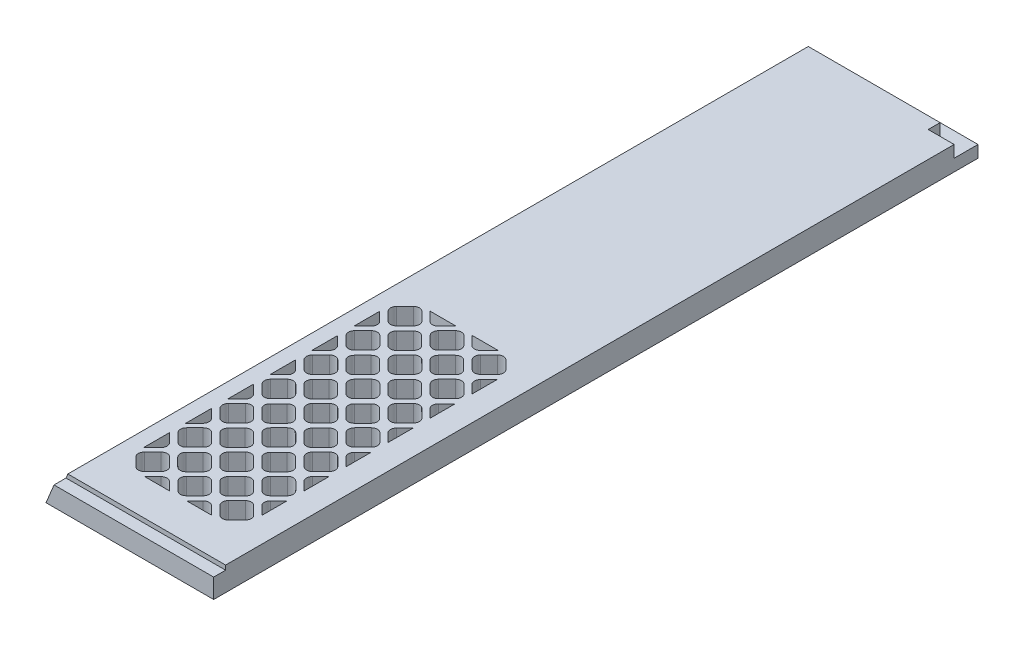
SolidWorks part; units mm, degrees
ref_plane "Front Plane" through (0, 0, 0) normal (0, 0, 1) x (1, 0, 0)
ref_plane "Top Plane" through (0, 0, 0) normal (0, 1, 0) x (1, 0, 0)
ref_plane "Right Plane" through (0, 0, 0) normal (1, 0, 0) x (0, 0, -1)
sketch "Sketch1" plane through (0, 0, 0) normal (0, 0, 1) x (1, 0, 0)
  line L0 (0, 0) -> (5.2605, 12.7)
  line L1 (5.2605, 12.7) -> (89.154, 12.7)
  line L2 (89.154, 12.7) -> (89.154, 0)
  line L3 (89.154, 0) -> (0, 0)
  dimension "D1" = 12.7
  dimension "D2" = 89.154
  dimension "D3" = 67.5
extrude "Boss-Extrude1" add sketch "Sketch1" along normal blind 406.4
sketch "Sketch2" plane through (0, 12.7, 0) normal (0, -1, 0) x (1, 0, 0)
  line L5 (89.154, 406.4) -> (89.154, 0) construction
  line L6 (0, 406.4) -> (89.154, 406.4)
  line L7 (0, 406.4) -> (0, 400.05)
  line L8 (0, 400.05) -> (89.154, 400.05)
  line L9 (89.154, 406.4) -> (89.154, 400.05)
  dimension "D2" = 6.35
extrude "Cut-Extrude1" cut sketch "Sketch2" along normal blind 2.3622
sketch "Sketch3" plane through (0, 0, 0) normal (0, -1, 0) x (1, 0, 0)
  line L90 (0, 203.2) -> (89.154, 203.2) construction
  line L91 (0, 406.4) -> (0, 0) construction
  line L221 (89.154, 406.4) -> (89.154, 0) construction
  line L222 (13.3842, 233.4919) -> (17.8743, 229.0018)
  line L223 (17.8743, 246.8637) -> (13.3842, 242.3736)
  line L235 (13.3842, 255.8439) -> (17.8743, 251.3538)
  line L236 (17.8743, 269.2157) -> (13.3842, 264.7256)
  line L237 (13.3842, 278.1959) -> (17.8743, 273.7058)
  line L238 (17.8743, 291.5677) -> (13.3842, 287.0776)
  line L239 (13.3842, 300.5479) -> (17.8743, 296.0578)
  line L240 (17.8743, 313.9197) -> (13.3842, 309.4296)
  line L241 (13.3842, 322.8999) -> (17.8743, 318.4098)
  line L242 (17.8743, 336.2717) -> (13.3842, 331.7816)
  line L243 (13.3842, 345.2519) -> (17.8743, 340.7618)
  line L244 (17.8743, 358.6237) -> (13.3842, 354.1336)
  line L245 (13.3842, 367.6039) -> (17.8743, 363.1138)
  line L246 (71.4599, 229.0018) -> (75.9093, 233.4512)
  line L247 (49.1079, 229.0018) -> (53.598, 233.4919)
  line L248 (58.0882, 233.4919) -> (62.5783, 229.0018)
  line L249 (26.7559, 229.0018) -> (31.246, 233.4919)
  line L250 (35.7362, 233.4919) -> (40.2263, 229.0018)
  line L251 (71.4599, 251.3538) -> (75.9093, 255.8032)
  line L252 (75.9093, 242.4143) -> (71.4599, 246.8637)
  line L253 (49.1079, 251.3538) -> (53.598, 255.8439)
  line L254 (53.598, 242.3736) -> (49.1079, 246.8637)
  line L255 (62.5783, 246.8637) -> (58.0882, 242.3736)
  line L256 (58.0882, 255.8439) -> (62.5783, 251.3538)
  line L257 (26.7559, 251.3538) -> (31.246, 255.8439)
  line L258 (31.246, 242.3736) -> (26.7559, 246.8637)
  line L259 (40.2263, 246.8637) -> (35.7362, 242.3736)
  line L260 (35.7362, 255.8439) -> (40.2263, 251.3538)
  line L261 (71.4599, 273.7058) -> (75.9093, 278.1552)
  line L262 (75.9093, 264.7663) -> (71.4599, 269.2157)
  line L263 (49.1079, 273.7058) -> (53.598, 278.1959)
  line L264 (53.598, 264.7256) -> (49.1079, 269.2157)
  line L265 (62.5783, 269.2157) -> (58.0882, 264.7256)
  line L266 (58.0882, 278.1959) -> (62.5783, 273.7058)
  line L267 (26.7559, 273.7058) -> (31.246, 278.1959)
  line L268 (31.246, 264.7256) -> (26.7559, 269.2157)
  line L269 (40.2263, 269.2157) -> (35.7362, 264.7256)
  line L270 (35.7362, 278.1959) -> (40.2263, 273.7058)
  line L271 (71.4599, 296.0578) -> (75.9093, 300.5072)
  line L272 (75.9093, 287.1183) -> (71.4599, 291.5677)
  line L273 (49.1079, 296.0578) -> (53.598, 300.5479)
  line L274 (53.598, 287.0776) -> (49.1079, 291.5677)
  line L275 (62.5783, 291.5677) -> (58.0882, 287.0776)
  line L276 (58.0882, 300.5479) -> (62.5783, 296.0578)
  line L277 (26.7559, 296.0578) -> (31.246, 300.5479)
  line L278 (31.246, 287.0776) -> (26.7559, 291.5677)
  line L279 (40.2263, 291.5677) -> (35.7362, 287.0776)
  line L280 (35.7362, 300.5479) -> (40.2263, 296.0578)
  line L281 (71.4599, 318.4098) -> (75.9093, 322.8592)
  line L282 (75.9093, 309.4703) -> (71.4599, 313.9197)
  line L283 (49.1079, 318.4098) -> (53.598, 322.8999)
  line L284 (53.598, 309.4296) -> (49.1079, 313.9197)
  line L285 (62.5783, 313.9197) -> (58.0882, 309.4296)
  line L286 (58.0882, 322.8999) -> (62.5783, 318.4098)
  line L287 (26.7559, 318.4098) -> (31.246, 322.8999)
  line L288 (31.246, 309.4296) -> (26.7559, 313.9197)
  line L289 (40.2263, 313.9197) -> (35.7362, 309.4296)
  line L290 (35.7362, 322.8999) -> (40.2263, 318.4098)
  line L291 (71.4599, 340.7618) -> (75.9093, 345.2112)
  line L292 (75.9093, 331.8223) -> (71.4599, 336.2717)
  line L293 (49.1079, 340.7618) -> (53.598, 345.2519)
  line L294 (53.598, 331.7816) -> (49.1079, 336.2717)
  line L295 (62.5783, 336.2717) -> (58.0882, 331.7816)
  line L296 (58.0882, 345.2519) -> (62.5783, 340.7618)
  line L297 (26.7559, 340.7618) -> (31.246, 345.2519)
  line L298 (31.246, 331.7816) -> (26.7559, 336.2717)
  line L299 (40.2263, 336.2717) -> (35.7362, 331.7816)
  line L300 (35.7362, 345.2519) -> (40.2263, 340.7618)
  line L301 (71.4599, 363.1138) -> (75.9093, 367.5632)
  line L302 (75.9093, 354.1743) -> (71.4599, 358.6237)
  line L303 (49.1079, 363.1138) -> (53.598, 367.6039)
  line L304 (53.598, 354.1336) -> (49.1079, 358.6237)
  line L305 (62.5783, 358.6237) -> (58.0882, 354.1336)
  line L306 (58.0882, 367.6039) -> (62.5783, 363.1138)
  line L307 (26.7559, 363.1138) -> (31.246, 367.6039)
  line L308 (31.246, 354.1336) -> (26.7559, 358.6237)
  line L309 (40.2263, 358.6237) -> (35.7362, 354.1336)
  line L310 (35.7362, 367.6039) -> (40.2263, 363.1138)
  line L311 (75.9093, 376.5263) -> (71.5993, 380.8363)
  line L312 (53.598, 376.4856) -> (49.2473, 380.8363)
  line L313 (62.4389, 380.8363) -> (58.0882, 376.4856)
  line L314 (31.246, 376.4856) -> (26.8953, 380.8363)
  line L315 (40.0869, 380.8363) -> (35.7362, 376.4856)
  line L316 (17.7349, 380.8363) -> (13.3842, 376.4856)
  line L317 (73.6642, 235.4989) -> (69.1741, 231.0088)
  line L318 (69.1741, 244.4792) -> (73.6642, 239.9891)
  line L319 (60.1938, 239.9891) -> (64.6839, 244.4792)
  line L320 (64.6839, 231.0088) -> (60.1938, 235.4989)
  line L321 (51.3122, 235.4989) -> (46.8221, 231.0088)
  line L322 (46.8221, 244.4792) -> (51.3122, 239.9891)
  line L323 (37.8418, 239.9891) -> (42.3319, 244.4792)
  line L324 (42.3319, 231.0088) -> (37.8418, 235.4989)
  line L325 (28.9602, 235.4989) -> (24.4701, 231.0088)
  line L326 (24.4701, 244.4792) -> (28.9602, 239.9891)
  line L327 (15.4898, 239.9891) -> (19.9799, 244.4792)
  line L328 (19.9799, 231.0088) -> (15.4898, 235.4989)
  line L329 (73.6642, 257.8509) -> (69.1741, 253.3608)
  line L330 (69.1741, 266.8312) -> (73.6642, 262.3411)
  line L331 (60.1938, 262.3411) -> (64.6839, 266.8312)
  line L332 (64.6839, 253.3608) -> (60.1938, 257.8509)
  line L333 (51.3122, 257.8509) -> (46.8221, 253.3608)
  line L334 (46.8221, 266.8312) -> (51.3122, 262.3411)
  line L335 (37.8418, 262.3411) -> (42.3319, 266.8312)
  line L336 (42.3319, 253.3608) -> (37.8418, 257.8509)
  line L337 (28.9602, 257.8509) -> (24.4701, 253.3608)
  line L338 (24.4701, 266.8312) -> (28.9602, 262.3411)
  line L339 (15.4898, 262.3411) -> (19.9799, 266.8312)
  line L340 (19.9799, 253.3608) -> (15.4898, 257.8509)
  line L341 (73.6642, 280.2029) -> (69.1741, 275.7128)
  line L342 (69.1741, 289.1832) -> (73.6642, 284.6931)
  line L343 (60.1938, 284.6931) -> (64.6839, 289.1832)
  line L344 (64.6839, 275.7128) -> (60.1938, 280.2029)
  line L345 (51.3122, 280.2029) -> (46.8221, 275.7128)
  line L346 (46.8221, 289.1832) -> (51.3122, 284.6931)
  line L347 (37.8418, 284.6931) -> (42.3319, 289.1832)
  line L348 (42.3319, 275.7128) -> (37.8418, 280.2029)
  line L349 (28.9602, 280.2029) -> (24.4701, 275.7128)
  line L350 (24.4701, 289.1832) -> (28.9602, 284.6931)
  line L351 (15.4898, 284.6931) -> (19.9799, 289.1832)
  line L352 (19.9799, 275.7128) -> (15.4898, 280.2029)
  line L353 (73.6642, 302.5549) -> (69.1741, 298.0648)
  line L354 (69.1741, 311.5352) -> (73.6642, 307.0451)
  line L355 (60.1938, 307.0451) -> (64.6839, 311.5352)
  line L356 (64.6839, 298.0648) -> (60.1938, 302.5549)
  line L357 (51.3122, 302.5549) -> (46.8221, 298.0648)
  line L358 (46.8221, 311.5352) -> (51.3122, 307.0451)
  line L359 (37.8418, 307.0451) -> (42.3319, 311.5352)
  line L360 (42.3319, 298.0648) -> (37.8418, 302.5549)
  line L361 (28.9602, 302.5549) -> (24.4701, 298.0648)
  line L362 (24.4701, 311.5352) -> (28.9602, 307.0451)
  line L363 (15.4898, 307.0451) -> (19.9799, 311.5352)
  line L364 (19.9799, 298.0648) -> (15.4898, 302.5549)
  line L365 (73.6642, 324.9069) -> (69.1741, 320.4168)
  line L366 (69.1741, 333.8872) -> (73.6642, 329.3971)
  line L367 (60.1938, 329.3971) -> (64.6839, 333.8872)
  line L368 (64.6839, 320.4168) -> (60.1938, 324.9069)
  line L369 (51.3122, 324.9069) -> (46.8221, 320.4168)
  line L370 (46.8221, 333.8872) -> (51.3122, 329.3971)
  line L371 (37.8418, 329.3971) -> (42.3319, 333.8872)
  line L372 (42.3319, 320.4168) -> (37.8418, 324.9069)
  line L373 (28.9602, 324.9069) -> (24.4701, 320.4168)
  line L374 (24.4701, 333.8872) -> (28.9602, 329.3971)
  line L375 (15.4898, 329.3971) -> (19.9799, 333.8872)
  line L376 (19.9799, 320.4168) -> (15.4898, 324.9069)
  line L377 (73.6642, 347.2589) -> (69.1741, 342.7688)
  line L378 (69.1741, 356.2392) -> (73.6642, 351.7491)
  line L379 (60.1938, 351.7491) -> (64.6839, 356.2392)
  line L380 (64.6839, 342.7688) -> (60.1938, 347.2589)
  line L381 (51.3122, 347.2589) -> (46.8221, 342.7688)
  line L382 (46.8221, 356.2392) -> (51.3122, 351.7491)
  line L383 (37.8418, 351.7491) -> (42.3319, 356.2392)
  line L384 (42.3319, 342.7688) -> (37.8418, 347.2589)
  line L385 (28.9602, 347.2589) -> (24.4701, 342.7688)
  line L386 (24.4701, 356.2392) -> (28.9602, 351.7491)
  line L387 (15.4898, 351.7491) -> (19.9799, 356.2392)
  line L388 (19.9799, 342.7688) -> (15.4898, 347.2589)
  line L389 (73.6642, 369.6109) -> (69.1741, 365.1208)
  line L390 (69.1741, 378.5912) -> (73.6642, 374.1011)
  line L391 (60.1938, 374.1011) -> (64.6839, 378.5912)
  line L392 (64.6839, 365.1208) -> (60.1938, 369.6109)
  line L393 (51.3122, 369.6109) -> (46.8221, 365.1208)
  line L394 (46.8221, 378.5912) -> (51.3122, 374.1011)
  line L395 (37.8418, 374.1011) -> (42.3319, 378.5912)
  line L396 (42.3319, 365.1208) -> (37.8418, 369.6109)
  line L397 (19.9799, 365.1208) -> (15.4898, 369.6109)
  line L398 (28.9602, 369.6109) -> (24.4701, 365.1208)
  line L399 (24.4701, 378.5912) -> (28.9602, 374.1011)
  line L400 (75.9093, 380.8363) -> (75.9093, 228.7637)
  line L401 (13.2447, 228.7637) -> (75.9093, 228.7637)
  line L402 (13.2447, 380.8363) -> (13.2447, 228.7637)
  line L403 (13.2447, 380.8363) -> (75.9093, 380.8363)
  line L404 (15.4898, 374.1011) -> (19.9799, 378.5912)
  arc A212 (18.0894, 228.7637) -> (17.8743, 229.0018) centre (15.6292, 226.7568) ccw
  arc A224 (13.2447, 233.6232) -> (13.3842, 233.4919) centre (11.1391, 231.2469) cw
  arc A225 (13.3842, 242.3736) -> (13.2447, 242.2423) centre (11.1391, 244.6186) cw
  arc A226 (17.8743, 246.8637) -> (17.8743, 251.3538) centre (15.6292, 249.1088) ccw
  arc A227 (13.2447, 255.9752) -> (13.3842, 255.8439) centre (11.1391, 253.5989) cw
  arc A228 (13.3842, 264.7256) -> (13.2447, 264.5943) centre (11.1391, 266.9706) cw
  arc A229 (17.8743, 269.2157) -> (17.8743, 273.7058) centre (15.6292, 271.4608) ccw
  arc A230 (13.2447, 278.3272) -> (13.3842, 278.1959) centre (11.1391, 275.9509) cw
  arc A231 (13.3842, 287.0776) -> (13.2447, 286.9463) centre (11.1391, 289.3226) cw
  arc A232 (17.8743, 291.5677) -> (17.8743, 296.0578) centre (15.6292, 293.8128) ccw
  arc A233 (13.2447, 300.6792) -> (13.3842, 300.5479) centre (11.1391, 298.3029) cw
  arc A234 (13.3842, 309.4296) -> (13.2447, 309.2983) centre (11.1391, 311.6746) cw
  arc A235 (17.8743, 313.9197) -> (17.8743, 318.4098) centre (15.6292, 316.1648) ccw
  arc A236 (13.2447, 323.0312) -> (13.3842, 322.8999) centre (11.1391, 320.6549) cw
  arc A237 (13.3842, 331.7816) -> (13.2447, 331.6503) centre (11.1391, 334.0266) cw
  arc A238 (17.8743, 336.2717) -> (17.8743, 340.7618) centre (15.6292, 338.5168) ccw
  arc A239 (13.2447, 345.3832) -> (13.3842, 345.2519) centre (11.1391, 343.0069) cw
  arc A240 (13.3842, 354.1336) -> (13.2447, 354.0023) centre (11.1391, 356.3786) cw
  arc A241 (17.8743, 358.6237) -> (17.8743, 363.1138) centre (15.6292, 360.8688) ccw
  arc A242 (13.2447, 367.7352) -> (13.3842, 367.6039) centre (11.1391, 365.3589) cw
  arc A243 (71.2448, 228.7637) -> (71.4599, 229.0018) centre (73.705, 226.7568) cw
  arc A244 (48.8928, 228.7637) -> (49.1079, 229.0018) centre (51.353, 226.7568) cw
  arc A245 (62.7934, 228.7637) -> (62.5783, 229.0018) centre (60.3332, 226.7568) ccw
  arc A246 (53.598, 233.4919) -> (58.0882, 233.4919) centre (55.8431, 231.2469) cw
  arc A247 (26.5408, 228.7637) -> (26.7559, 229.0018) centre (29.001, 226.7568) cw
  arc A248 (40.4414, 228.7637) -> (40.2263, 229.0018) centre (37.9812, 226.7568) ccw
  arc A249 (31.246, 233.4919) -> (35.7362, 233.4919) centre (33.4911, 231.2469) cw
  arc A250 (71.4599, 246.8637) -> (71.4599, 251.3538) centre (73.705, 249.1088) cw
  arc A251 (49.1079, 246.8637) -> (49.1079, 251.3538) centre (51.353, 249.1088) cw
  arc A252 (58.0882, 242.3736) -> (53.598, 242.3736) centre (55.8431, 244.6186) cw
  arc A253 (62.5783, 246.8637) -> (62.5783, 251.3538) centre (60.3332, 249.1088) ccw
  arc A254 (53.598, 255.8439) -> (58.0882, 255.8439) centre (55.8431, 253.5989) cw
  arc A255 (26.7559, 246.8637) -> (26.7559, 251.3538) centre (29.001, 249.1088) cw
  arc A256 (35.7362, 242.3736) -> (31.246, 242.3736) centre (33.4911, 244.6186) cw
  arc A257 (40.2263, 246.8637) -> (40.2263, 251.3538) centre (37.9812, 249.1088) ccw
  arc A258 (31.246, 255.8439) -> (35.7362, 255.8439) centre (33.4911, 253.5989) cw
  arc A259 (71.4599, 269.2157) -> (71.4599, 273.7058) centre (73.705, 271.4608) cw
  arc A260 (49.1079, 269.2157) -> (49.1079, 273.7058) centre (51.353, 271.4608) cw
  arc A261 (58.0882, 264.7256) -> (53.598, 264.7256) centre (55.8431, 266.9706) cw
  arc A262 (62.5783, 269.2157) -> (62.5783, 273.7058) centre (60.3332, 271.4608) ccw
  arc A263 (53.598, 278.1959) -> (58.0882, 278.1959) centre (55.8431, 275.9509) cw
  arc A264 (26.7559, 269.2157) -> (26.7559, 273.7058) centre (29.001, 271.4608) cw
  arc A265 (35.7362, 264.7256) -> (31.246, 264.7256) centre (33.4911, 266.9706) cw
  arc A266 (40.2263, 269.2157) -> (40.2263, 273.7058) centre (37.9812, 271.4608) ccw
  arc A267 (31.246, 278.1959) -> (35.7362, 278.1959) centre (33.4911, 275.9509) cw
  arc A268 (71.4599, 291.5677) -> (71.4599, 296.0578) centre (73.705, 293.8128) cw
  arc A269 (49.1079, 291.5677) -> (49.1079, 296.0578) centre (51.353, 293.8128) cw
  arc A270 (58.0882, 287.0776) -> (53.598, 287.0776) centre (55.8431, 289.3226) cw
  arc A271 (62.5783, 291.5677) -> (62.5783, 296.0578) centre (60.3332, 293.8128) ccw
  arc A272 (53.598, 300.5479) -> (58.0882, 300.5479) centre (55.8431, 298.3029) cw
  arc A273 (26.7559, 291.5677) -> (26.7559, 296.0578) centre (29.001, 293.8128) cw
  arc A274 (35.7362, 287.0776) -> (31.246, 287.0776) centre (33.4911, 289.3226) cw
  arc A275 (40.2263, 291.5677) -> (40.2263, 296.0578) centre (37.9812, 293.8128) ccw
  arc A276 (31.246, 300.5479) -> (35.7362, 300.5479) centre (33.4911, 298.3029) cw
  arc A277 (71.4599, 313.9197) -> (71.4599, 318.4098) centre (73.705, 316.1648) cw
  arc A278 (49.1079, 313.9197) -> (49.1079, 318.4098) centre (51.353, 316.1648) cw
  arc A279 (58.0882, 309.4296) -> (53.598, 309.4296) centre (55.8431, 311.6746) cw
  arc A280 (62.5783, 313.9197) -> (62.5783, 318.4098) centre (60.3332, 316.1648) ccw
  arc A281 (53.598, 322.8999) -> (58.0882, 322.8999) centre (55.8431, 320.6549) cw
  arc A282 (26.7559, 313.9197) -> (26.7559, 318.4098) centre (29.001, 316.1648) cw
  arc A283 (35.7362, 309.4296) -> (31.246, 309.4296) centre (33.4911, 311.6746) cw
  arc A284 (40.2263, 313.9197) -> (40.2263, 318.4098) centre (37.9812, 316.1648) ccw
  arc A285 (31.246, 322.8999) -> (35.7362, 322.8999) centre (33.4911, 320.6549) cw
  arc A286 (71.4599, 336.2717) -> (71.4599, 340.7618) centre (73.705, 338.5168) cw
  arc A287 (49.1079, 336.2717) -> (49.1079, 340.7618) centre (51.353, 338.5168) cw
  arc A288 (58.0882, 331.7816) -> (53.598, 331.7816) centre (55.8431, 334.0266) cw
  arc A289 (62.5783, 336.2717) -> (62.5783, 340.7618) centre (60.3332, 338.5168) ccw
  arc A290 (53.598, 345.2519) -> (58.0882, 345.2519) centre (55.8431, 343.0069) cw
  arc A291 (26.7559, 336.2717) -> (26.7559, 340.7618) centre (29.001, 338.5168) cw
  arc A292 (35.7362, 331.7816) -> (31.246, 331.7816) centre (33.4911, 334.0266) cw
  arc A293 (40.2263, 336.2717) -> (40.2263, 340.7618) centre (37.9812, 338.5168) ccw
  arc A294 (31.246, 345.2519) -> (35.7362, 345.2519) centre (33.4911, 343.0069) cw
  arc A295 (71.4599, 358.6237) -> (71.4599, 363.1138) centre (73.705, 360.8688) cw
  arc A296 (49.1079, 358.6237) -> (49.1079, 363.1138) centre (51.353, 360.8688) cw
  arc A297 (58.0882, 354.1336) -> (53.598, 354.1336) centre (55.8431, 356.3786) cw
  arc A298 (62.5783, 358.6237) -> (62.5783, 363.1138) centre (60.3332, 360.8688) ccw
  arc A299 (53.598, 367.6039) -> (58.0882, 367.6039) centre (55.8431, 365.3589) cw
  arc A300 (26.7559, 358.6237) -> (26.7559, 363.1138) centre (29.001, 360.8688) cw
  arc A301 (35.7362, 354.1336) -> (31.246, 354.1336) centre (33.4911, 356.3786) cw
  arc A302 (40.2263, 358.6237) -> (40.2263, 363.1138) centre (37.9812, 360.8688) ccw
  arc A303 (31.246, 367.6039) -> (35.7362, 367.6039) centre (33.4911, 365.3589) cw
  arc A304 (58.0882, 376.4856) -> (53.598, 376.4856) centre (55.8431, 378.7306) cw
  arc A305 (35.7362, 376.4856) -> (31.246, 376.4856) centre (33.4911, 378.7306) cw
  arc A306 (13.3842, 376.4856) -> (13.2447, 376.3543) centre (11.1391, 378.7306) cw
  arc A307 (69.1741, 231.0088) -> (64.6839, 231.0088) centre (66.929, 233.2539) cw
  arc A308 (73.6642, 239.9891) -> (73.6642, 235.4989) centre (71.4191, 237.744) cw
  arc A309 (64.6839, 244.4792) -> (69.1741, 244.4792) centre (66.929, 242.2341) cw
  arc A310 (60.1938, 239.9891) -> (60.1938, 235.4989) centre (62.4389, 237.744) ccw
  arc A311 (46.8221, 231.0088) -> (42.3319, 231.0088) centre (44.577, 233.2539) cw
  arc A312 (51.3122, 239.9891) -> (51.3122, 235.4989) centre (49.0671, 237.744) cw
  arc A313 (42.3319, 244.4792) -> (46.8221, 244.4792) centre (44.577, 242.2341) cw
  arc A314 (37.8418, 239.9891) -> (37.8418, 235.4989) centre (40.0869, 237.744) ccw
  arc A315 (28.9602, 239.9891) -> (28.9602, 235.4989) centre (26.7151, 237.744) cw
  arc A316 (19.9799, 244.4792) -> (24.4701, 244.4792) centre (22.225, 242.2341) cw
  arc A317 (24.4701, 231.0088) -> (19.9799, 231.0088) centre (22.225, 233.2539) cw
  arc A318 (15.4898, 239.9891) -> (15.4898, 235.4989) centre (17.7349, 237.744) ccw
  arc A319 (69.1741, 253.3608) -> (64.6839, 253.3608) centre (66.929, 255.6059) cw
  arc A320 (73.6642, 262.3411) -> (73.6642, 257.8509) centre (71.4191, 260.096) cw
  arc A321 (64.6839, 266.8312) -> (69.1741, 266.8312) centre (66.929, 264.5861) cw
  arc A322 (60.1938, 262.3411) -> (60.1938, 257.8509) centre (62.4389, 260.096) ccw
  arc A323 (46.8221, 253.3608) -> (42.3319, 253.3608) centre (44.577, 255.6059) cw
  arc A324 (51.3122, 262.3411) -> (51.3122, 257.8509) centre (49.0671, 260.096) cw
  arc A325 (42.3319, 266.8312) -> (46.8221, 266.8312) centre (44.577, 264.5861) cw
  arc A326 (37.8418, 262.3411) -> (37.8418, 257.8509) centre (40.0869, 260.096) ccw
  arc A327 (28.9602, 262.3411) -> (28.9602, 257.8509) centre (26.7151, 260.096) cw
  arc A328 (19.9799, 266.8312) -> (24.4701, 266.8312) centre (22.225, 264.5861) cw
  arc A329 (24.4701, 253.3608) -> (19.9799, 253.3608) centre (22.225, 255.6059) cw
  arc A330 (15.4898, 262.3411) -> (15.4898, 257.8509) centre (17.7349, 260.096) ccw
  arc A331 (69.1741, 275.7128) -> (64.6839, 275.7128) centre (66.929, 277.9579) cw
  arc A332 (73.6642, 284.6931) -> (73.6642, 280.2029) centre (71.4191, 282.448) cw
  arc A333 (64.6839, 289.1832) -> (69.1741, 289.1832) centre (66.929, 286.9381) cw
  arc A334 (60.1938, 284.6931) -> (60.1938, 280.2029) centre (62.4389, 282.448) ccw
  arc A335 (46.8221, 275.7128) -> (42.3319, 275.7128) centre (44.577, 277.9579) cw
  arc A336 (51.3122, 284.6931) -> (51.3122, 280.2029) centre (49.0671, 282.448) cw
  arc A337 (42.3319, 289.1832) -> (46.8221, 289.1832) centre (44.577, 286.9381) cw
  arc A338 (37.8418, 284.6931) -> (37.8418, 280.2029) centre (40.0869, 282.448) ccw
  arc A339 (28.9602, 284.6931) -> (28.9602, 280.2029) centre (26.7151, 282.448) cw
  arc A340 (19.9799, 289.1832) -> (24.4701, 289.1832) centre (22.225, 286.9381) cw
  arc A341 (24.4701, 275.7128) -> (19.9799, 275.7128) centre (22.225, 277.9579) cw
  arc A342 (15.4898, 284.6931) -> (15.4898, 280.2029) centre (17.7349, 282.448) ccw
  arc A343 (69.1741, 298.0648) -> (64.6839, 298.0648) centre (66.929, 300.3099) cw
  arc A344 (73.6642, 307.0451) -> (73.6642, 302.5549) centre (71.4191, 304.8) cw
  arc A345 (64.6839, 311.5352) -> (69.1741, 311.5352) centre (66.929, 309.2901) cw
  arc A346 (60.1938, 307.0451) -> (60.1938, 302.5549) centre (62.4389, 304.8) ccw
  arc A347 (46.8221, 298.0648) -> (42.3319, 298.0648) centre (44.577, 300.3099) cw
  arc A348 (51.3122, 307.0451) -> (51.3122, 302.5549) centre (49.0671, 304.8) cw
  arc A349 (42.3319, 311.5352) -> (46.8221, 311.5352) centre (44.577, 309.2901) cw
  arc A350 (37.8418, 307.0451) -> (37.8418, 302.5549) centre (40.0869, 304.8) ccw
  arc A351 (28.9602, 307.0451) -> (28.9602, 302.5549) centre (26.7151, 304.8) cw
  arc A352 (19.9799, 311.5352) -> (24.4701, 311.5352) centre (22.225, 309.2901) cw
  arc A353 (24.4701, 298.0648) -> (19.9799, 298.0648) centre (22.225, 300.3099) cw
  arc A354 (15.4898, 307.0451) -> (15.4898, 302.5549) centre (17.7349, 304.8) ccw
  arc A355 (69.1741, 320.4168) -> (64.6839, 320.4168) centre (66.929, 322.6619) cw
  arc A356 (73.6642, 329.3971) -> (73.6642, 324.9069) centre (71.4191, 327.152) cw
  arc A357 (64.6839, 333.8872) -> (69.1741, 333.8872) centre (66.929, 331.6421) cw
  arc A358 (60.1938, 329.3971) -> (60.1938, 324.9069) centre (62.4389, 327.152) ccw
  arc A359 (46.8221, 320.4168) -> (42.3319, 320.4168) centre (44.577, 322.6619) cw
  arc A360 (51.3122, 329.3971) -> (51.3122, 324.9069) centre (49.0671, 327.152) cw
  arc A361 (42.3319, 333.8872) -> (46.8221, 333.8872) centre (44.577, 331.6421) cw
  arc A362 (37.8418, 329.3971) -> (37.8418, 324.9069) centre (40.0869, 327.152) ccw
  arc A363 (28.9602, 329.3971) -> (28.9602, 324.9069) centre (26.7151, 327.152) cw
  arc A364 (19.9799, 333.8872) -> (24.4701, 333.8872) centre (22.225, 331.6421) cw
  arc A365 (24.4701, 320.4168) -> (19.9799, 320.4168) centre (22.225, 322.6619) cw
  arc A366 (15.4898, 329.3971) -> (15.4898, 324.9069) centre (17.7349, 327.152) ccw
  arc A367 (69.1741, 342.7688) -> (64.6839, 342.7688) centre (66.929, 345.0139) cw
  arc A368 (73.6642, 351.7491) -> (73.6642, 347.2589) centre (71.4191, 349.504) cw
  arc A369 (64.6839, 356.2392) -> (69.1741, 356.2392) centre (66.929, 353.9941) cw
  arc A370 (60.1938, 351.7491) -> (60.1938, 347.2589) centre (62.4389, 349.504) ccw
  arc A371 (46.8221, 342.7688) -> (42.3319, 342.7688) centre (44.577, 345.0139) cw
  arc A372 (51.3122, 351.7491) -> (51.3122, 347.2589) centre (49.0671, 349.504) cw
  arc A373 (42.3319, 356.2392) -> (46.8221, 356.2392) centre (44.577, 353.9941) cw
  arc A374 (37.8418, 351.7491) -> (37.8418, 347.2589) centre (40.0869, 349.504) ccw
  arc A375 (28.9602, 351.7491) -> (28.9602, 347.2589) centre (26.7151, 349.504) cw
  arc A376 (19.9799, 356.2392) -> (24.4701, 356.2392) centre (22.225, 353.9941) cw
  arc A377 (24.4701, 342.7688) -> (19.9799, 342.7688) centre (22.225, 345.0139) cw
  arc A378 (15.4898, 351.7491) -> (15.4898, 347.2589) centre (17.7349, 349.504) ccw
  arc A379 (73.6642, 374.1011) -> (73.6642, 369.6109) centre (71.4191, 371.856) cw
  arc A380 (64.6839, 378.5912) -> (69.1741, 378.5912) centre (66.929, 376.3461) cw
  arc A381 (69.1741, 365.1208) -> (64.6839, 365.1208) centre (66.929, 367.3659) cw
  arc A382 (60.1938, 374.1011) -> (60.1938, 369.6109) centre (62.4389, 371.856) ccw
  arc A383 (51.3122, 374.1011) -> (51.3122, 369.6109) centre (49.0671, 371.856) cw
  arc A384 (42.3319, 378.5912) -> (46.8221, 378.5912) centre (44.577, 376.3461) cw
  arc A385 (46.8221, 365.1208) -> (42.3319, 365.1208) centre (44.577, 367.3659) cw
  arc A386 (37.8418, 374.1011) -> (37.8418, 369.6109) centre (40.0869, 371.856) ccw
  arc A387 (15.4898, 374.1011) -> (15.4898, 369.6109) centre (17.7349, 371.856) ccw
  arc A388 (19.9799, 378.5912) -> (24.4701, 378.5912) centre (22.225, 376.3461) cw
  arc A389 (24.4701, 365.1208) -> (19.9799, 365.1208) centre (22.225, 367.3659) cw
  arc A390 (28.9602, 374.1011) -> (28.9602, 369.6109) centre (26.7151, 371.856) cw
  point P1134 (2.1589, 383.2208)
  point P1135 (11.1391, 392.201)
  point P1136 (20.1194, 383.2208)
  point P1137 (13.2447, 371.856)
  point P1138 (22.225, 380.8363)
  point P1139 (31.2053, 371.856)
extrude "Cut-Extrude2" cut sketch "Sketch3" against normal through all contours A390 L399 A388 L404 A387 L397 A389 L398 | L395 A386 L396 A385 L393 A383 L394 A384 | L391 A382 L392 A381 L389 A379 L390 A380 | A299 L303 A296 L304 A297 L305 A298 L306 | A303 L307 A300 L308 A301 L309 A302 L310 | L387 A378 L388 A377 L385 A375 L386 A376 | L383 A374 L384 A371 L381 A372 L382 A373 | L379 A370 L380 A367 L377 A368 L378 A369 | A290 L293 A287 L294 A288 L295 A289 L296 | A294 L297 A291 L298 A292 L299 A293 L300 | L375 A366 L376 A365 L373 A363 L374 A364 | L371 A362 L372 A359 L369 A360 L370 A361 | L367 A358 L368 A355 L365 A356 L366 A357 | A285 L287 A282 L288 A283 L289 A284 L290 | A281 L283 A278 L284 A279 L285 A280 L286 | L363 A354 L364 A353 L361 A351 L362 A352 | L359 A350 L360 A347 L357 A348 L358 A349 | L355 A346 L356 A343 L353 A344 L354 A345 | A272 L273 A269 L274 A270 L275 A271 L276 | A276 L277 A273 L278 A274 L279 A275 L280 | L351 A342 L352 A341 L349 A339 L350 A340 | L339 A330 L340 A329 L337 A327 L338 A328 | L327 A318 L328 A317 L325 A315 L326 A316 | A258 L257 A255 L258 A256 L259 A257 L260 | A267 L267 A264 L268 A265 L269 A266 L270 | L347 A338 L348 A335 L345 A336 L346 A337 | L335 A326 L336 A323 L333 A324 L334 A325 | L323 A314 L324 A311 L321 A312 L322 A313 | A263 L263 A260 L264 A261 L265 A262 L266 | L343 A334 L344 A331 L341 A332 L342 A333 | L331 A322 L332 A319 L329 A320 L330 A321 | A254 L253 A251 L254 A252 L255 A253 L256 | L319 A310 L320 A307 L317 A308 L318 A309 | A242 L402 A240 L244 A241 L245 | A239 L402 A237 L242 A238 L243 | A236 L402 A234 L240 A235 L241 | A305 L315 L403 L314 | A304 L313 L403 L312 | A295 L302 L400 L301 | A286 L292 L400 L291 | A277 L282 L400 L281 | A268 L272 L400 L271 | A233 L402 A231 L238 A232 L239 | A259 L262 L400 L261 | A250 L252 L400 L251 | A246 L247 A244 L401 A245 L248 | A249 L249 A247 L401 A248 L250 | A227 L402 A225 L223 A226 L235 | A230 L402 A228 L236 A229 L237
sketch "Sketch4" plane through (0, 12.7, 0) normal (0, 1, 0) x (1, 0, 0)
  line L1 (89.154, 0) -> (-9.1024, 0)
  line L2 (89.154, 0) -> (89.154, -6.35)
  line L3 (75.3689, -6.35) -> (-9.1024, -6.35)
  line L4 (-9.1024, 0) -> (-9.1024, -6.35)
  line L6 (89.154, -6.35) -> (89.154, -12.7)
  line L7 (89.154, -12.7) -> (75.3689, -12.7)
  line L8 (75.3689, -6.35) -> (75.3689, -12.7)
  dimension "D1" = 6.35
  dimension "D2" = 6.35
extrude "Cut-Extrude3" cut sketch "Sketch4" against normal blind 6.35
